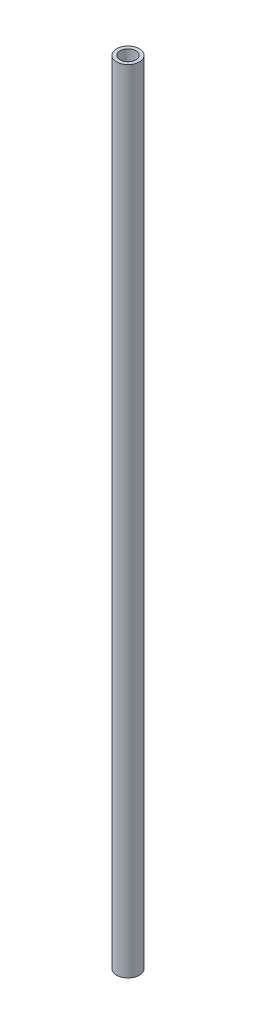
SolidWorks part; units mm, degrees
ref_plane "Front Plane" through (0, 0, 0) normal (0, 0, 1) x (1, 0, 0)
ref_plane "Top Plane" through (0, 0, 0) normal (0, 1, 0) x (1, 0, 0)
ref_plane "Right Plane" through (0, 0, 0) normal (1, 0, 0) x (0, 0, -1)
sketch "Sketch1" plane through (0, 0, 0) normal (0, 1, 0) x (1, 0, 0)
  circle A0 centre (0, 0) radius 3.75
  dimension "D1" = 7.5
extrude "Boss-Extrude1" add sketch "Sketch1" along normal blind 260
sketch "Sketch2" plane through (0, 260, 0) normal (0, 1, 0) x (1, 0, 0)
  circle A0 centre (0, 0) radius 2.6
  dimension "D1" = 5.2
extrude "Cut-Extrude2" cut sketch "Sketch2" against normal through all contours A0
